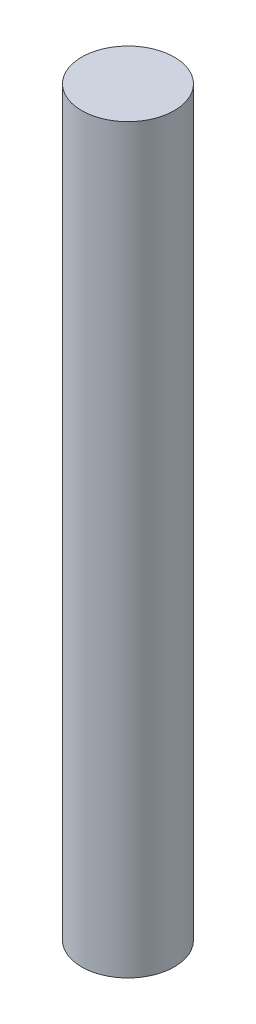
SolidWorks part; units mm, degrees
material "ABS"
ref_plane "Front Plane" through (0, 0, 0) normal (0, 0, 1) x (1, 0, 0)
ref_plane "Top Plane" through (0, 0, 0) normal (0, 1, 0) x (1, 0, 0)
ref_plane "Right Plane" through (0, 0, 0) normal (1, 0, 0) x (0, 0, -1)
sketch "Sketch1" plane through (0, 0, 0) normal (0, 1, 0) x (1, 0, 0)
  circle A0 centre (0, 0) radius 2.5
  dimension "D1" = 5
extrude "Boss-Extrude1" add sketch "Sketch1" along normal mid plane 40
